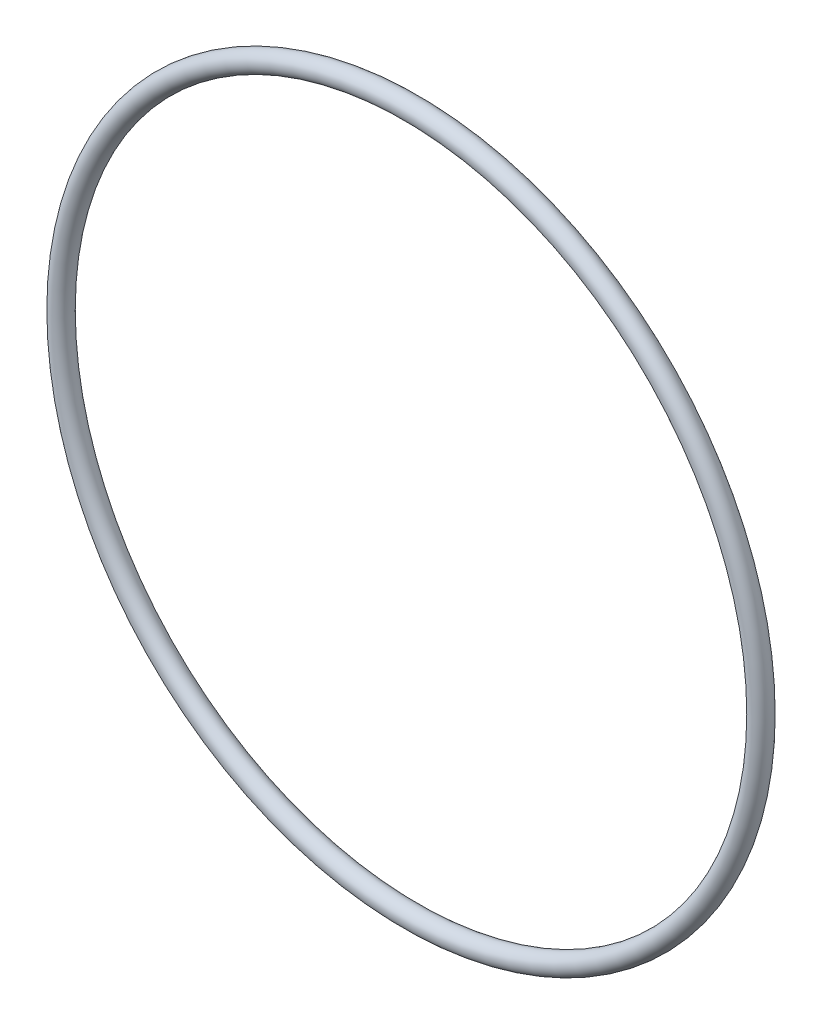
SolidWorks part; units mm, degrees
ref_plane "Front Plane" through (0, 0, 0) normal (0, 0, 1) x (1, 0, 0)
ref_plane "Top Plane" through (0, 0, 0) normal (0, 1, 0) x (1, 0, 0)
ref_plane "Right Plane" through (0, 0, 0) normal (1, 0, 0) x (0, 0, -1)
sketch "SketchPath" plane through (0, 0, 0) normal (0, 0, 1) x (1, 0, 0)
  circle A0 centre (0, 0) radius 55.245
  dimension "D1" = 110.49
sweep "Base Sweep" add path "SketchPath" circular profile diameter 3.175 parameters "D3"=3.175
